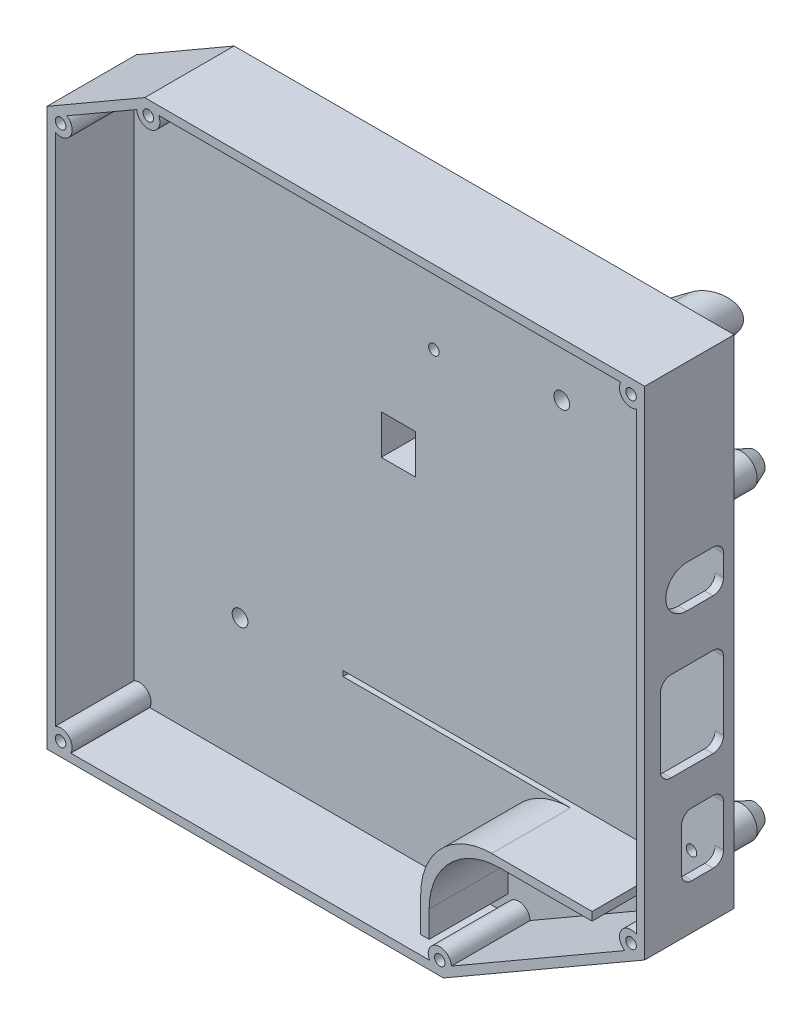
SolidWorks part; units mm, degrees
ref_plane "Front Plane" through (0, 0, 0) normal (0, 0, 1) x (1, 0, 0)
ref_plane "Top Plane" through (0, 0, 0) normal (0, 1, 0) x (1, 0, 0)
ref_plane "Right Plane" through (0, 0, 0) normal (1, 0, 0) x (0, 0, -1)
sketch "Sketch1" plane through (0, 0, 0) normal (0, 0, 1) x (1, 0, 0)
  line L0 (-25, 227.5) -> (25, 227.5) construction
  line L1 (25, 200) -> (-25, 200)
  line L2 (25, 200) -> (25, 255)
  line L3 (25, 255) -> (-25, 255)
  line L4 (-25, 200) -> (-25, 255)
  line L5 (0, 255) -> (0, 200) construction
  line L6 (-16, 246.25) -> (17, 246.25) construction
  line L7 (-16, 246.25) -> (-16, 208.75) construction
  line L8 (-16, 246.25) -> (-16, 255) construction
  line L9 (-16, 208.75) -> (-16, 200) construction
  circle A0 centre (-16, 246.25) radius 1
  circle A1 centre (17, 246.25) radius 1
  circle A2 centre (-16, 208.75) radius 1
  circle A3 centre (17, 208.75) radius 1
  point P4 (0, 255)
  point P5 (0, 200)
  dimension "D4" = 2
  dimension "D7" = 2
  dimension "D1" = 55
  dimension "D2" = 50
  dimension "D3" = 200
  dimension "D5" = 16
  dimension "D6" = 37.5
  dimension "D8" = 17
ref_plane "Plane1" through (0, 0, 8) normal (0, 0, 1) x (1, 0, 0)
sketch "Sketch2" plane through (0, 0, 8) normal (0, 0, 1) x (1, 0, 0)
  line L4 (-25, 200) -> (25, 200)
  line L5 (-25, 255) -> (-25, 200)
  line L6 (25, 255) -> (-25, 255)
  line L7 (25, 200) -> (25, 255)
  line L8 (-25, 200) -> (-9.5, 200)
  line L9 (-25, 255) -> (-25, 200)
  line L10 (25, 255) -> (-25, 255)
  line L11 (25, 200) -> (25, 255)
  line L12 (0, 255) -> (0, 200) construction
  line L13 (-2.25, 235.5) -> (4.25, 235.5)
  line L14 (-2.25, 235.5) -> (-2.25, 243)
  line L15 (-2.25, 243) -> (4.25, 243)
  line L16 (4.25, 235.5) -> (4.25, 243)
  line L17 (-2.25, 235.5) -> (4.25, 243) construction
  line L18 (-2.25, 243) -> (4.25, 235.5) construction
  line L19 (0, 255) -> (0, 200) construction
  line L20 (13.5, 200) -> (25, 200)
  line L22 (-9.5, 200) -> (-9.5, 204)
  line L23 (-9.5, 204) -> (9.5, 204)
  line L24 (9.5, 200) -> (9.5, 204) construction
  line L25 (92.3839, 281.75) -> (92.3839, 173.25) construction
  line L26 (-44.75, 234.25) -> (19.25, 234.25) construction
  line L27 (-44.75, 234.25) -> (-44.75, 173.25) construction
  line L28 (-44.75, 173.25) -> (19.25, 173.25) construction
  line L29 (19.25, 234.25) -> (19.25, 173.25) construction
  line L30 (5.25, 281.75) -> (61.25, 281.75) construction
  line L31 (5.25, 281.75) -> (5.25, 196.75) construction
  line L32 (5.25, 196.75) -> (61.25, 196.75) construction
  line L33 (61.25, 281.75) -> (61.25, 196.75) construction
  line L34 (9.5, 204) -> (13.5, 200)
  circle A0 centre (10.5, 218.75) radius 1
  circle A1 centre (17, 246.25) radius 1
  circle A2 centre (17, 246.25) radius 1
  circle A3 centre (-16, 246.25) radius 1
  circle A4 centre (-16, 246.25) radius 1
  circle A5 centre (17, 208.75) radius 1
  circle A6 centre (17, 208.75) radius 1
  circle A7 centre (-16, 208.75) radius 1
  circle A8 centre (-16, 208.75) radius 1
  circle A9 centre (10.5, 231.25) radius 1
  circle A10 centre (-10.5, 218.75) radius 1
  circle A11 centre (-10.5, 231.25) radius 1
  point P20 (1, 239.25)
  point P21 (1, 239.25)
  point P30 (0, 204)
  point P49 (92.3839, 227.5)
  dimension "D13" = 2
  dimension "D7" = 17
  dimension "D8" = 7
  dimension "D9" = 6.5
  dimension "D10" = 7.5
  dimension "D11" = 6.5
  dimension "D12" = 10
  dimension "D14" = 12.5
  dimension "D6" = 19
  dimension "D15" = 4
  dimension "D16" = 56
  dimension "D17" = 85
  dimension "D18" = 64
  dimension "D19" = 61
  dimension "D20" = 14
  dimension "D21" = 23.5
  dimension "D22" = 45
  dimension "D23" = 1
  dimension "D24" = 21
  dimension "D1" = 0
  dimension "D2" = 0
  dimension "D3" = 0
  dimension "D4" = 0
  dimension "D5" = 0
extrude "Boss-Extrude1" add sketch "Sketch2" along normal blind 2
sketch "Sketch3" plane through (0, 0, 10) normal (0, 0, 1) x (1, 0, 0)
  line L0 (-2.25, 235.5) -> (4.25, 235.5) construction
  line L1 (-2.25, 243) -> (-2.25, 235.5) construction
  line L2 (4.25, 235.5) -> (4.25, 243) construction
  line L3 (4.25, 243) -> (-2.25, 243) construction
  line L4 (-2.25, 235.5) -> (4.25, 235.5)
  line L5 (-2.25, 243) -> (-2.25, 235.5)
  line L6 (4.25, 235.5) -> (4.25, 243)
  line L7 (4.25, 243) -> (-2.25, 243)
  line L8 (-3.25, 234.5) -> (5.25, 234.5)
  line L9 (5.25, 234.5) -> (5.25, 244)
  line L10 (5.25, 244) -> (-3.25, 244)
  line L11 (-3.25, 244) -> (-3.25, 234.5)
  circle A0 centre (-16, 246.25) radius 1 construction
  circle A1 centre (-10.5, 231.25) radius 1 construction
  circle A2 centre (-10.5, 218.75) radius 1 construction
  circle A3 centre (-16, 208.75) radius 1 construction
  circle A4 centre (17, 208.75) radius 1 construction
  circle A5 centre (10.5, 218.75) radius 1 construction
  circle A6 centre (10.5, 231.25) radius 1 construction
  circle A7 centre (17, 246.25) radius 1 construction
  circle A8 centre (-16, 246.25) radius 1
  circle A9 centre (-10.5, 231.25) radius 1
  circle A10 centre (-10.5, 218.75) radius 1
  circle A11 centre (-16, 208.75) radius 1
  circle A12 centre (17, 208.75) radius 1
  circle A13 centre (10.5, 218.75) radius 1
  circle A14 centre (10.5, 231.25) radius 1
  circle A15 centre (17, 246.25) radius 1
  circle A16 centre (-16, 246.25) radius 2
  circle A17 centre (-10.5, 231.25) radius 2
  circle A18 centre (-10.5, 218.75) radius 2
  circle A19 centre (-16, 208.75) radius 2
  circle A20 centre (17, 208.75) radius 2
  circle A21 centre (10.5, 218.75) radius 2
  circle A22 centre (10.5, 231.25) radius 2
  circle A23 centre (17, 246.25) radius 2
  dimension "D1" = 1
  dimension "D2" = 1
  dimension "D3" = 1
extrude "Boss-Extrude2" add sketch "Sketch3" along normal blind 7
sketch "Sketch4" plane through (0, 0, 17) normal (0, 0, 1) x (1, 0, 0)
  line L0 (4.25, 235.5) -> (4.25, 243) construction
  line L1 (5.25, 196.75) -> (61.25, 196.75) construction
  line L2 (-44.75, 173.25) -> (19.25, 173.25) construction
  line L3 (-44.75, 234.25) -> (-44.75, 173.25) construction
  line L4 (-50.85, 276.5113) -> (-32.25, 287.25)
  line L6 (52.85, 195.75) -> (52.85, 196.75)
  line L7 (52.85, 196.75) -> (-9.5, 196.75)
  line L8 (-50.85, 276.5113) -> (-50.85, 170.65)
  line L9 (4.25, 281.75) -> (4.25, 196.75) construction
  line L11 (-50.85, 170.65) -> (24.5717, 170.65)
  line L17 (62.85, 192.75) -> (62.85, 287.25)
  line L19 (62.85, 287.25) -> (-32.25, 287.25)
  line L20 (24.5717, 170.65) -> (62.85, 192.75)
  line L21 (20.25, 175.65) -> (20.25, 182.25) construction
  line L22 (33.75, 195.75) -> (52.85, 195.75) construction
  line L23 (52.85, 195.75) -> (52.85, 194.15) construction
  line L24 (52.85, 194.15) -> (35.35, 194.15) construction
  line L25 (21.85, 180.65) -> (21.85, 175.65) construction
  line L26 (21.85, 175.65) -> (20.25, 175.65)
  line L27 (19.25, 234.25) -> (19.25, 173.25) construction
  line L28 (-9.5, 195.75) -> (52.85, 195.75)
  line L30 (5.25, 281.75) -> (5.25, 196.75) construction
  line L31 (-2.25, 243) -> (4.25, 243) construction
  line L32 (-2.25, 235.5) -> (-2.25, 243) construction
  line L33 (-2.25, 235.5) -> (4.25, 235.5) construction
  line L34 (4.25, 235.5) -> (4.25, 243)
  line L35 (-2.25, 235.5) -> (4.25, 235.5)
  line L36 (-2.25, 235.5) -> (-2.25, 243)
  line L37 (-2.25, 243) -> (4.25, 243)
  line L38 (5.25, 281.75) -> (61.25, 281.75) construction
  line L40 (61.25, 281.75) -> (61.25, 196.75) construction
  line L44 (-9.5, 196.75) -> (-9.5, 195.75)
  circle A0 centre (7.75, 258.25) radius 1
  circle A1 centre (56.75, 258.25) radius 1
  circle A2 centre (56.75, 200.25) radius 1
  circle A3 centre (7.75, 200.25) radius 1 construction
  arc A4 (20.25, 182.25) -> (33.75, 195.75) centre (33.75, 182.25) cw construction
  arc A5 (35.35, 194.15) -> (21.85, 180.65) centre (35.35, 180.65) ccw construction
  point P28 (52.85, 194.95)
  dimension "D2" = 2
  dimension "D16" = 13.5
  dimension "D3" = 49
  dimension "D4" = 58
  dimension "D5" = 3.5
  dimension "D6" = 3.5
  dimension "D8" = 1
  dimension "D9" = 1
  dimension "D10" = 1.6
  dimension "D11" = 1.6
  dimension "D12" = 10
  dimension "D13" = 5
  dimension "D7" = 2.6
  dimension "D14" = 6.1
  dimension "D15" = 30
  dimension "D17" = 5.5
  dimension "D18" = 37.5
  dimension "D19" = 1.6
  dimension "D20" = 4
extrude "Boss-Extrude4" add sketch "Sketch4" along normal blind 2 contours L17 L19 L4 L8 L11 L20 | A1 | A2 | L7 L44 L28 L6 | A0 | L35 L34 L37 L36 | A3
sketch "Sketch5" plane through (0, 0, 19) normal (0, 0, 1) x (1, 0, 0)
  line L0 (20.25, 175.65) -> (20.25, 182.25) construction
  line L1 (21.85, 175.65) -> (20.25, 175.65) construction
  line L2 (21.85, 180.65) -> (21.85, 175.65) construction
  line L3 (52.85, 195.75) -> (52.85, 194.15) construction
  line L4 (52.85, 194.15) -> (35.35, 194.15) construction
  line L5 (20.25, 175.65) -> (20.25, 182.25)
  line L6 (21.85, 175.65) -> (20.25, 175.65)
  line L7 (21.85, 180.65) -> (21.85, 175.65)
  line L8 (52.85, 195.75) -> (52.85, 194.15)
  line L9 (52.85, 194.15) -> (35.35, 194.15)
  line L10 (24.5717, 170.65) -> (62.85, 192.75) construction
  line L11 (-50.85, 170.65) -> (24.5717, 170.65) construction
  line L12 (-50.85, 276.5113) -> (-50.85, 170.65) construction
  line L13 (-50.85, 276.5113) -> (-32.25, 287.25) construction
  line L14 (62.85, 287.25) -> (-32.25, 287.25) construction
  line L15 (62.85, 192.75) -> (62.85, 287.25) construction
  line L16 (24.5717, 170.65) -> (62.85, 192.75)
  line L17 (-50.85, 170.65) -> (24.5717, 170.65)
  line L18 (-50.85, 276.5113) -> (-50.85, 170.65)
  line L19 (-50.85, 276.5113) -> (-32.25, 287.25)
  line L20 (62.85, 287.25) -> (-32.25, 287.25)
  line L21 (62.85, 192.75) -> (62.85, 287.25)
  line L25 (-46.2904, 172.25) -> (21.9154, 172.25)
  line L26 (26.0721, 173.3638) -> (59.0529, 192.4053)
  line L27 (61.25, 196.2107) -> (61.25, 282.6904)
  line L28 (-47.0529, 276.856) -> (-33.7504, 284.5362)
  line L29 (-49.25, 275.5875) -> (-31.8213, 285.65) construction
  line L30 (-49.25, 273.0506) -> (-49.25, 175.2096)
  line L31 (-49.25, 275.5875) -> (-49.25, 172.25) construction
  line L32 (-47.0529, 276.856) -> (-49.25, 275.5875) construction
  line L33 (-49.25, 275.5875) -> (-49.25, 273.0506) construction
  line L34 (61.25, 285.65) -> (-31.8213, 285.65) construction
  line L35 (58.2904, 285.65) -> (-29.5937, 285.65)
  line L36 (61.25, 193.6738) -> (61.25, 285.65) construction
  line L37 (-49.25, 175.2096) -> (-49.25, 173.25) construction
  line L38 (24.143, 172.25) -> (61.25, 193.6738) construction
  line L39 (-49.25, 172.25) -> (24.143, 172.25) construction
  line L40 (-46.2904, 172.25) -> (-48.25, 172.25) construction
  line L41 (-33.7504, 284.5362) -> (-32.0533, 285.516) construction
  line L42 (-29.5937, 285.65) -> (-31.5533, 285.65) construction
  line L43 (58.2904, 285.65) -> (60.25, 285.65) construction
  line L44 (61.25, 282.6904) -> (61.25, 284.65) construction
  arc A0 (35.35, 194.15) -> (21.85, 180.65) centre (35.35, 180.65) ccw construction
  arc A1 (33.75, 195.75) -> (20.25, 182.25) centre (33.75, 182.25) ccw construction
  arc A2 (35.35, 194.15) -> (21.85, 180.65) centre (35.35, 180.65) ccw
  arc A3 (33.75, 195.75) -> (20.25, 182.25) centre (33.75, 182.25) ccw
  circle A4 centre (-48.25, 275.0102) radius 1
  arc A5 (-49.25, 273.0506) -> (-47.0529, 276.856) centre (-48.25, 275.0102) ccw
  circle A6 centre (-48.25, 173.25) radius 1
  arc A7 (-46.2904, 172.25) -> (-49.25, 175.2096) centre (-48.25, 173.25) ccw
  circle A8 centre (23.875, 173.25) radius 1
  arc A9 (26.0721, 173.3638) -> (21.9154, 172.25) centre (23.875, 173.25) ccw
  circle A10 centre (60.25, 284.65) radius 1
  arc A11 (58.2904, 285.65) -> (61.25, 282.6904) centre (60.25, 284.65) ccw
  circle A12 centre (60.25, 194.2511) radius 1
  arc A13 (61.25, 196.2107) -> (59.0529, 192.4053) centre (60.25, 194.2511) ccw
  circle A14 centre (-31.5533, 284.65) radius 1
  arc A15 (-33.7504, 284.5362) -> (-29.5937, 285.65) centre (-31.5533, 284.65) ccw
  circle A16 centre (-48.25, 275.0102) radius 2.2 construction
  point P50 (-49.25, 275.5875)
  line M9 (24.5717, 170.65) -> (62.85, 192.75)
  line M10 (62.85, 192.75) -> (62.85, 287.25)
  line M11 (62.85, 287.25) -> (-32.25, 287.25)
  line M12 (-32.25, 287.25) -> (-50.85, 276.5113)
  line M13 (-50.85, 276.5113) -> (-50.85, 170.65)
  line M14 (-50.85, 170.65) -> (24.5717, 170.65)
  line M18 (52.85, 195.75) -> (-9.5, 195.75)
  dimension "D2" = 2
  dimension "D4" = 1.6
  dimension "D5" = 1.6
  dimension "D6" = 1.6
  dimension "D1" = 1.6
  dimension "D3" = 1.2
extrude "Boss-Extrude5" add sketch "Sketch5" along normal blind 15 contours A4 A6 A8 A10 A12 A14 L28 A15 L35 A11 L27 A13 L26 A9 L25 A7 L30 A5 M14 M9 M10 M11 M12 M13 | A3 L5 L6 L7 A2 L9 L8 M18
sketch "Sketch6" plane through (0, 0, 17) normal (0, 0, -1) x (-1, 0, 0)
  line L0 (-58.95, 274.75) -> (-58.95, 200.602)
  line L1 (-55.2, 194.1068) -> (-24.9723, 176.6548)
  line L2 (-21.2223, 175.65) -> (38.35, 175.65)
  line L3 (45.85, 183.15) -> (45.85, 269.2944)
  line L4 (42.1, 275.7896) -> (32.6506, 281.2452)
  line L5 (28.9006, 282.25) -> (-51.45, 282.25)
  line L6 (-62.85, 287.25) -> (32.25, 287.25) construction
  line L7 (50.85, 276.5113) -> (32.25, 287.25) construction
  line L8 (50.85, 276.5113) -> (50.85, 170.65) construction
  line L9 (50.85, 170.65) -> (-24.5717, 170.65) construction
  line L10 (-24.5717, 170.65) -> (-62.85, 192.75) construction
  line L11 (38.1, 273.4802) -> (31.5788, 277.2452)
  line L12 (27.8288, 278.25) -> (-47.45, 278.25)
  line L13 (-54.95, 270.75) -> (-54.95, 202.9114)
  line L14 (-51.2, 196.4162) -> (-23.9005, 180.6548)
  line L15 (-20.1505, 179.65) -> (34.35, 179.65)
  line L16 (41.85, 187.15) -> (41.85, 266.985)
  line L17 (20, 255) -> (5, 255) construction
  line L18 (-25, 200) -> (-25, 225) construction
  line L19 (-25, 200) -> (-25, 255) construction
  line L20 (-25, 255) -> (25, 255) construction
  line L21 (25, 255) -> (25, 215) construction
  line L22 (25, 200) -> (25, 255) construction
  line L23 (-25, 200) -> (-13.5, 200) construction
  line L24 (25, 215) -> (25, 200)
  line L25 (25, 200) -> (9.5, 200)
  line L26 (-25, 225) -> (-25, 255)
  line L27 (-25, 255) -> (5, 255)
  line L28 (-54.95, 278.25) -> (-54.95, 198.5812) construction
  line L29 (-54.95, 198.5812) -> (-22.1601, 179.65) construction
  line L30 (-58.95, 282.25) -> (-58.95, 196.2718) construction
  line L31 (-58.95, 196.2718) -> (-23.2319, 175.65) construction
  line L32 (-22.1601, 179.65) -> (41.85, 179.65) construction
  line L33 (-23.2319, 175.65) -> (45.85, 175.65) construction
  line L34 (45.85, 175.65) -> (45.85, 273.6245) construction
  line L35 (41.85, 179.65) -> (41.85, 271.3151) construction
  line L36 (41.85, 271.3151) -> (29.8385, 278.25) construction
  line L37 (45.85, 273.6245) -> (30.9103, 282.25) construction
  line L38 (29.8385, 278.25) -> (-54.95, 278.25) construction
  line L39 (30.9103, 282.25) -> (-58.95, 282.25) construction
  line L40 (-7.2964, 256.2) -> (26.2, 256.2)
  line L41 (26.2, 256.2) -> (26.2, 207.6398)
  line L42 (-26.2, 237.2964) -> (-26.2, 198.8)
  line L43 (-26.2, 198.8) -> (-14.7, 198.8)
  line L44 (25, 215) -> (25, 255)
  line L45 (-13.5, 200) -> (-25, 200) construction
  line L46 (-25, 225) -> (-25, 200)
  line L47 (-25, 200) -> (-13.5, 200)
  line L48 (25, 255) -> (5, 255)
  line L49 (-13.5, 200) -> (-14.7, 198.8)
  line L50 (9.5, 200) -> (9.5, 198.8)
  line L51 (-9.5, 204) -> (-13.5, 200) construction
  line L52 (9.5, 198.8) -> (16.8602, 198.8)
  arc A0 (-29.8775, 265.416) -> (-35.416, 259.8775) centre (-32.0711, 262.0711) ccw
  circle A1 centre (-56.75, 200.25) radius 1 construction
  circle A2 centre (-56.75, 258.25) radius 1 construction
  circle A3 centre (-56.75, 200.25) radius 1
  circle A4 centre (-56.75, 258.25) radius 1
  arc A5 (5, 255) -> (-29.8775, 265.416) centre (5, 318.6011) cw
  arc A6 (-25, 225) -> (-35.416, 259.8775) centre (-88.6011, 225) ccw
  arc A7 (26.2265, 192.8642) -> (31.9195, 198.4836) centre (29.1139, 195.6324) ccw
  arc A8 (9.5, 200) -> (26.2265, 192.8642) centre (9.5, 176.8283) cw
  arc A9 (25, 215) -> (31.9195, 198.4836) centre (48.1717, 215) ccw
  circle A10 centre (29.1139, 195.6324) radius 1.5
  circle A11 centre (-32.0711, 262.0711) radius 1.5
  arc A12 (-54.95, 202.9114) -> (-51.2, 196.4162) centre (-47.45, 202.9114) ccw
  arc A13 (-58.95, 200.602) -> (-55.2, 194.1068) centre (-51.45, 200.602) ccw
  arc A14 (-23.9005, 180.6548) -> (-20.1505, 179.65) centre (-20.1505, 187.15) ccw
  arc A15 (-24.9723, 176.6548) -> (-21.2223, 175.65) centre (-21.2223, 183.15) ccw
  arc A16 (38.35, 175.65) -> (45.85, 183.15) centre (38.35, 183.15) ccw
  arc A17 (34.35, 179.65) -> (41.85, 187.15) centre (34.35, 187.15) ccw
  arc A18 (38.1, 273.4802) -> (41.85, 266.985) centre (34.35, 266.985) cw
  arc A19 (45.85, 269.2944) -> (42.1, 275.7896) centre (38.35, 269.2944) ccw
  arc A20 (31.5788, 277.2452) -> (27.8288, 278.25) centre (27.8288, 270.75) ccw
  arc A21 (32.6506, 281.2452) -> (28.9006, 282.25) centre (28.9006, 274.75) ccw
  arc A22 (-47.45, 278.25) -> (-54.95, 270.75) centre (-47.45, 270.75) ccw
  arc A23 (-58.95, 274.75) -> (-51.45, 282.25) centre (-51.45, 274.75) cw
  dimension "D2" = 5
  dimension "D10" = 8
  dimension "D11" = 3
  dimension "D15" = 7.5
  dimension "D1" = 2.2
  dimension "D3" = 5
  dimension "D4" = 5
  dimension "D5" = 5
  dimension "D6" = 5
  dimension "D8" = 30
  dimension "D9" = 30
  dimension "D12" = 10
  dimension "D13" = 15
  dimension "D14" = 6
  dimension "D16" = 1.2
  dimension "D17" = 1.2
  dimension "D18" = 1.2
  dimension "D19" = 1.2
  dimension "D7" = 4
extrude "Boss-Extrude6" add sketch "Sketch6" along normal up to surface (24.6738 mm away) contours A6 L26 L27 A5 A0 A11 | A9 L24 L25 A8 A7 A10 | L44 A9 L41 L40 A5 L48 | A8 L47 L17 L46 A6 L42 L43 | A8 L50 L52
sketch "Sketch7" plane through (0, 0, 10) normal (0, 0, 1) x (1, 0, 0)
  line L0 (-2.25, 243) -> (4.25, 243) construction
  line L1 (4.25, 235.5) -> (4.25, 243) construction
  line L2 (-2.25, 235.5) -> (4.25, 235.5) construction
  line L3 (-2.25, 235.5) -> (-2.25, 243) construction
  line L4 (-2.25, 243) -> (4.25, 243)
  line L5 (4.25, 235.5) -> (4.25, 243)
  line L6 (-2.25, 235.5) -> (4.25, 235.5)
  line L7 (-2.25, 235.5) -> (-2.25, 243)
  line L11 (13.5, 200) -> (25, 200)
  line L12 (13.5, 200) -> (25, 200)
  line L13 (25, 200) -> (25, 255)
  line L14 (25, 255) -> (-25, 255)
  line L17 (-25, 255) -> (-25, 200)
  line L18 (-25, 200) -> (-9.5, 200)
  line L19 (-9.5, 200) -> (-9.5, 204)
  line L20 (-9.5, 204) -> (9.5, 204)
  line L21 (9.5, 204) -> (13.5, 200)
  line L24 (25, 200) -> (25, 255)
  line L25 (25, 255) -> (-25, 255)
  line L28 (-25, 255) -> (-25, 200)
  line L29 (-25, 200) -> (-9.5, 200)
  line L30 (-9.5, 200) -> (-9.5, 204)
  line L31 (-9.5, 204) -> (9.5, 204)
  line L32 (9.5, 204) -> (13.5, 200)
  circle A0 centre (-16, 208.75) radius 1 construction
  circle A1 centre (-10.5, 218.75) radius 1 construction
  circle A2 centre (17, 208.75) radius 1 construction
  circle A3 centre (10.5, 218.75) radius 1 construction
  circle A4 centre (17, 246.25) radius 1 construction
  circle A5 centre (10.5, 231.25) radius 1 construction
  circle A6 centre (-10.5, 231.25) radius 1 construction
  circle A7 centre (-16, 246.25) radius 1 construction
  circle A8 centre (-16, 208.75) radius 1
  circle A9 centre (-10.5, 218.75) radius 1
  circle A10 centre (17, 208.75) radius 1
  circle A11 centre (10.5, 218.75) radius 1
  circle A12 centre (17, 246.25) radius 1
  circle A13 centre (10.5, 231.25) radius 1
  circle A14 centre (-10.5, 231.25) radius 1
  circle A15 centre (-16, 246.25) radius 1
  point P2 (-10.5, 231.25)
  dimension "D1" = 0
extrude "Boss-Extrude7" add sketch "Sketch7" along normal up to surface (7 mm away) up to face at (0.3177, 221.007, 17)
ref_plane "Plane2" through (7.75, 0, 0) normal (1, 0, 0) x (0, 0, -1)
sketch "Sketch8" plane through (7.75, 0, 0) normal (1, 0, 0) x (0, 0, -1)
  line L0 (-17, 258.25) -> (-7, 258.25) construction
  line L1 (-7, 259.25) -> (-7, 260.25)
  line L2 (-17, 275.2554) -> (-17, 262.25) construction
  line L3 (-17, 276.5113) -> (-17, 287.25) construction
  line L4 (-7, 260.25) -> (0.7167, 260.25) construction
  line L5 (-7, 259.25) -> (-17, 259.25)
  line L6 (-17, 259.25) -> (-17, 262.25)
  line L7 (-17, 262.25) -> (-14.5, 261.25)
  line L8 (-14.5, 261.25) -> (-9.5, 261.25)
  line L9 (-9.5, 261.25) -> (-7, 260.25)
  dimension "D1" = 10
  dimension "D2" = 2
  dimension "D3" = 1
  dimension "D4" = 1
  dimension "D5" = 3
  dimension "D6" = 5
revolve "Revolve1" add sketch "Sketch8" angle 360 about L0
ref_plane "Plane3" through (56.75, 0, 0) normal (1, 0, 0) x (0, 0, -1)
sketch "Sketch9" plane through (56.75, 0, 0) normal (1, 0, 0) x (0, 0, -1)
  line L0 (-17, 258.25) -> (-3.3133, 258.25) construction
  line L3 (-7, 259.25) -> (-7, 260.25)
  line L4 (-17, 262.25) -> (-17, 259.25)
  line L5 (-17, 259.25) -> (-7, 259.25)
  line L6 (-7, 259.25) -> (-7, 260.25)
  line L7 (-17, 262.25) -> (-17, 259.25)
  line L8 (-17, 259.25) -> (-7, 259.25)
  line L13 (-7, 260.25) -> (-9.5, 261.25)
  line L14 (-7, 260.25) -> (-9.5, 261.25)
  line L15 (-9.5, 261.25) -> (-14.5, 261.25)
  line L16 (-9.5, 261.25) -> (-14.5, 261.25)
  line L17 (-14.5, 261.25) -> (-17, 262.25)
  line L18 (-14.5, 261.25) -> (-17, 262.25)
  dimension "D1" = 0
revolve "Revolve3" add sketch "Sketch9" angle 360 about L0
ref_plane "Plane4" through (0, 200.25, 0) normal (0, -1, 0) x (-1, 0, 0)
sketch "Sketch10" plane through (0, 200.25, 0) normal (0, -1, 0) x (-1, 0, 0)
  line L0 (-55.75, -7) -> (-57.75, -7) construction
  line L1 (-55.75, -7) -> (-57.75, -7) construction
  line L2 (-55.75, -7) -> (-55.75, -17)
  line L3 (-62.85, -17) -> (32.25, -17) construction
  line L4 (-55.75, -17) -> (-52.75, -17)
  line L5 (-55.75, -7) -> (-54.75, -7)
  line L6 (-56.75, -7) -> (-56.75, -17) construction
  line L7 (-57.75, -17) -> (-55.75, -17) construction
  line L8 (-52.75, -17) -> (-53.75, -14.5) construction
  line L9 (-53.75, -14.5) -> (-53.75, -9.5) construction
  line L10 (-53.75, -9.5) -> (-54.75, -7) construction
  line L11 (-52.75, -17) -> (-53.75, -14.5)
  line L12 (-53.75, -14.5) -> (-53.75, -9.5)
  line L13 (-53.75, -9.5) -> (-54.75, -7)
revolve "Revolve4" add sketch "Sketch10" angle 360 about L6
sketch "Sketch11" plane through (0, 198.8, 0) normal (0, -1, 0) x (1, 0, 0)
  line L0 (9.5, 8) -> (13.5, 8) construction
  line L2 (14.7, 17) -> (9.5, 17) construction
  line L3 (-9.5, 8) -> (9.5, 8) construction
  line L6 (9.5, 8) -> (13.5, 8)
  line L8 (14.7, 17) -> (9.5, 17)
  line L9 (-9.5, 8) -> (9.5, 8)
  line L12 (-9.5, 8) -> (-9.5, -0.7321)
  line L13 (13.5, 8) -> (13.5, -1.4876)
  arc A0 (26.2, -5.8078) -> (14.7, -1.7679) centre (0, -62) ccw construction
  arc A1 (13.5, -1.4876) -> (-9.5, -0.7321) centre (0, -62) ccw
sketch "Sketch13" plane through (0, 0, 17) normal (0, 0, -1) x (-1, 0, 0)
  circle A0 centre (-32.0711, 262.0711) radius 1.5 construction
  circle A1 centre (29.1139, 195.6324) radius 1.5 construction
  circle A2 centre (-32.0711, 262.0711) radius 1.5
  circle A3 centre (29.1139, 195.6324) radius 1.5
extrude "Cut-Extrude3" cut sketch "Sketch13" against normal through all both and the other way through all
sketch "Sketch14" plane through (62.85, 0, 0) normal (1, 0, 0) x (0, 0, -1)
  line L0 (-19, 201.25) -> (-19, 199.25) construction
  line L1 (-19, 201.25) -> (-19, 199.25) construction
  line L2 (-19, 200.25) -> (-19, 207.35) construction
  line L3 (-26, 254.25) -> (-21, 254.25)
  line L4 (-21, 213.35) -> (-25, 213.35)
  line L5 (-19, 211.35) -> (-19, 203.35)
  line L6 (-21, 201.35) -> (-25, 201.35)
  line L7 (-27, 211.35) -> (-27, 203.35)
  line L8 (-29, 237.25) -> (-21, 237.25)
  line L9 (-31, 235.25) -> (-31, 222.25)
  line L10 (-29, 220.25) -> (-21, 220.25)
  line L11 (-19, 235.25) -> (-19, 222.25)
  line L12 (-22, 250.25) -> (-22, 268.5289) construction
  line L13 (-19, 252.25) -> (-19, 248.25)
  line L14 (-21, 246.25) -> (-26, 246.25)
  arc A0 (-25, 201.35) -> (-27, 203.35) centre (-25, 203.35) cw
  arc A1 (-19, 203.35) -> (-21, 201.35) centre (-21, 203.35) cw
  arc A2 (-21, 213.35) -> (-19, 211.35) centre (-21, 211.35) cw
  arc A3 (-25, 213.35) -> (-27, 211.35) centre (-25, 211.35) ccw
  arc A4 (-31, 222.25) -> (-29, 220.25) centre (-29, 222.25) ccw
  arc A5 (-21, 220.25) -> (-19, 222.25) centre (-21, 222.25) ccw
  arc A6 (-21, 237.25) -> (-19, 235.25) centre (-21, 235.25) cw
  arc A7 (-29, 237.25) -> (-31, 235.25) centre (-29, 235.25) ccw
  arc A8 (-26, 254.25) -> (-26, 246.25) centre (-26, 250.25) ccw
  arc A9 (-19, 248.25) -> (-21, 246.25) centre (-21, 248.25) cw
  arc A10 (-21, 254.25) -> (-19, 252.25) centre (-21, 252.25) cw
  point P8 (-19, 207.35)
  point P11 (-27, 201.35)
  point P14 (-19, 201.35)
  point P19 (-27, 213.35)
  point P24 (-19, 228.75)
  point P29 (-19, 220.25)
  point P32 (-19, 237.25)
  point P35 (-31, 237.25)
  dimension "D4" = 2
  dimension "D8" = 2
  dimension "D9" = 8
  dimension "D12" = 2
  dimension "D1" = 7.1
  dimension "D2" = 12
  dimension "D3" = 8
  dimension "D5" = 28.5
  dimension "D6" = 17
  dimension "D7" = 12
  dimension "D10" = 3
  dimension "D11" = 50
extrude "Cut-Extrude4" cut sketch "Sketch14" against normal up to surface (1.6 mm away) up to face at (61.25, 239.4506, 26.5)
